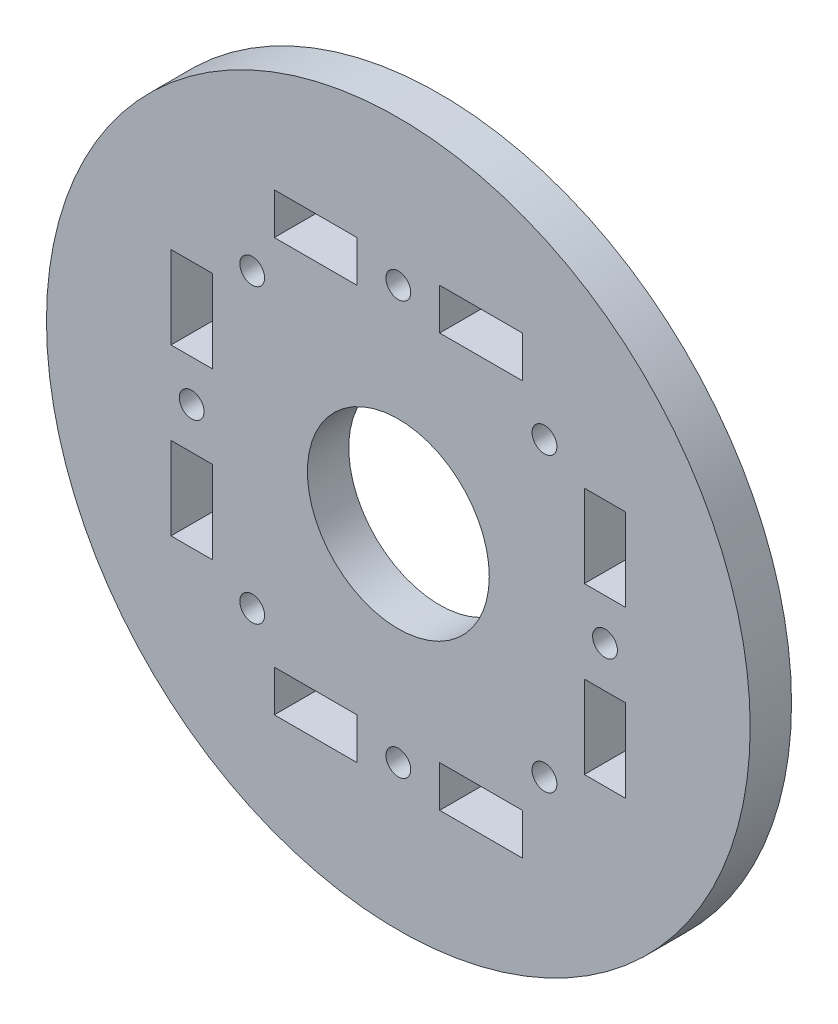
SolidWorks part; units mm, degrees
material "PMMA"
ref_plane "Front Plane" through (0, 0, 0) normal (0, 0, 1) x (1, 0, 0)
ref_plane "Top Plane" through (0, 0, 0) normal (0, 1, 0) x (1, 0, 0)
ref_plane "Right Plane" through (0, 0, 0) normal (1, 0, 0) x (0, 0, -1)
sketch "Schizzo1" plane through (0, 0, 0) normal (0, 0, 1) x (1, 0, 0)
  circle A1 centre (0, 0) radius 42.5627
  dimension "D2" = 85.1253
extrude "Estrusione-Estrusione1" add sketch "Schizzo1" along normal blind 5
sketch "Schizzo3" plane through (0, 0, 0) normal (0, 0, 1) x (1, 0, 0)
  circle A0 centre (0, 0) radius 11
  dimension "D1" = 22
extrude "Taglio-Estrusione2" cut sketch "Schizzo3" along direction (0, 0, 1) on the side of the normal through all
sketch "Schizzo4" plane through (0, 0, 0) normal (0, 0, 1) x (1, 0, 0)
  line L0 (-27.5, -15) -> (-27.5, -5)
  line L1 (0, 0) -> (0, 25) construction
  line L2 (0, -2.6008) -> (0, 40.6044) construction
  line L3 (0.0469, 0) -> (-50.6046, 0) construction
  line L4 (-27.5, 15) -> (-22.5, 15)
  line L5 (0, 0) -> (-22.5, 5) construction
  line L6 (-27.5, 15) -> (-27.5, 5)
  line L7 (-27.5, 5) -> (-22.5, 5)
  line L8 (-22.5, 15) -> (-22.5, 5)
  line L9 (-27.5, -5) -> (-22.5, -5)
  line L10 (-22.5, -15) -> (-22.5, -5)
  line L11 (-27.5, -15) -> (-22.5, -15)
  line L12 (5, 27.5) -> (5, 22.5)
  line L13 (15, 22.5) -> (5, 22.5)
  line L14 (15, 27.5) -> (15, 22.5)
  line L15 (15, 27.5) -> (5, 27.5)
  line L16 (-15, 22.5) -> (-5, 22.5)
  line L17 (-5, 27.5) -> (-5, 22.5)
  line L18 (-15, 27.5) -> (-5, 27.5)
  line L19 (-15, 27.5) -> (-15, 22.5)
  line L20 (27.5, -5) -> (22.5, -5)
  line L21 (22.5, -15) -> (22.5, -5)
  line L22 (27.5, -15) -> (22.5, -15)
  line L23 (27.5, -15) -> (27.5, -5)
  line L24 (22.5, 15) -> (22.5, 5)
  line L25 (27.5, 5) -> (22.5, 5)
  line L26 (27.5, 15) -> (27.5, 5)
  line L27 (27.5, 15) -> (22.5, 15)
  line L28 (-5, -27.5) -> (-5, -22.5)
  line L29 (-15, -22.5) -> (-5, -22.5)
  line L30 (-15, -27.5) -> (-15, -22.5)
  line L31 (-15, -27.5) -> (-5, -27.5)
  line L32 (15, -22.5) -> (5, -22.5)
  line L33 (5, -27.5) -> (5, -22.5)
  line L34 (15, -27.5) -> (5, -27.5)
  line L35 (15, -27.5) -> (15, -22.5)
  circle A8 centre (0, 25) radius 1.5
  circle A9 centre (17.6777, 17.6777) radius 1.5
  circle A10 centre (25, 0) radius 1.5
  circle A11 centre (17.6777, -17.6777) radius 1.5
  circle A12 centre (0, -25) radius 1.5
  circle A13 centre (-17.6777, -17.6777) radius 1.5
  circle A14 centre (-25, 0) radius 1.5
  circle A15 centre (-17.6777, 17.6777) radius 1.5
  point P0 (0, 0)
  point P15 (0, 0)
  point P54 (0, 0)
  dimension "D1" = 5
  dimension "D5" = 3
  dimension "D2" = 10
  dimension "D4" = 4
  dimension "D8" = 25
  dimension "D9" = 22.5
  dimension "D3" = 5
  dimension "D7" = 8
extrude "Taglio-Estrusione3" cut sketch "Schizzo4" along direction (0, 0, 1) on the side of the normal through all
equation "\"PD\"= ( \"Pitch\" * \"N\" ) / 3.141593'Pitch Diameter"
equation "\"Pitch\"= 8"
equation "\"N\"= 32'Number of Teeth"
equation "\"OD\"= \"PD\" - 2 * \"U\"'Outer Diameter"
equation "\"h_t\"= 3.451mm'Height of the tooth"
equation "\"D2@Schizzo1\"=\"OD\"+5mm"
equation "\"U\"= 0.681'distance between the tensile cord and the bottom of the belt tooth"
equation "\"Thickness5\"=5"
equation "\"D1@Estrusione-Estrusione1\"=\"Thickness5\""
equation "\"D_t\"=5.14"
equation "\"R\"=0.15"
equation "\"R_t\"=0.8"
equation "\"ID\"= \"OD\" - 2 * \"h_t\""
